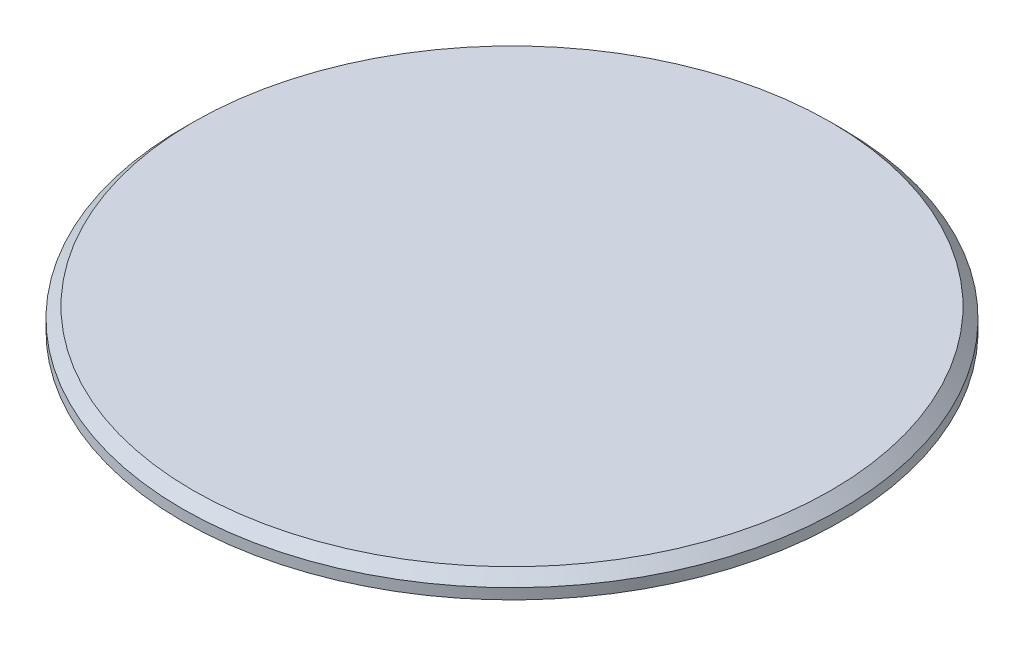
SolidWorks part; units mm, degrees
ref_plane "Front Plane" through (0, 0, 0) normal (0, 0, 1) x (1, 0, 0)
ref_plane "Top Plane" through (0, 0, 0) normal (0, 1, 0) x (1, 0, 0)
ref_plane "Right Plane" through (0, 0, 0) normal (1, 0, 0) x (0, 0, -1)
sketch "Sketch1" plane through (0, 0, 0) normal (0, 1, 0) x (1, 0, 0)
  circle A0 centre (0, 0) radius 17.35
extrude "Boss-Extrude1" add sketch "Sketch1" along normal blind 7
sketch "Sketch2" plane through (0, 7, 0) normal (0, 1, 0) x (1, 0, 0)
  circle A0 centre (0, 0) radius 31
extrude "Boss-Extrude2" add sketch "Sketch2" along normal blind 2
sketch "Sketch3" plane through (0, 0, 0) normal (0, -1, 0) x (1, 0, 0)
  circle A0 centre (0, 0) radius 14.6467
extrude "Cut-Extrude1" cut sketch "Sketch3" against normal blind 7
chamfer "Chamfer1" distance 1 angle 45 1 edges at (0, 9, 31)
